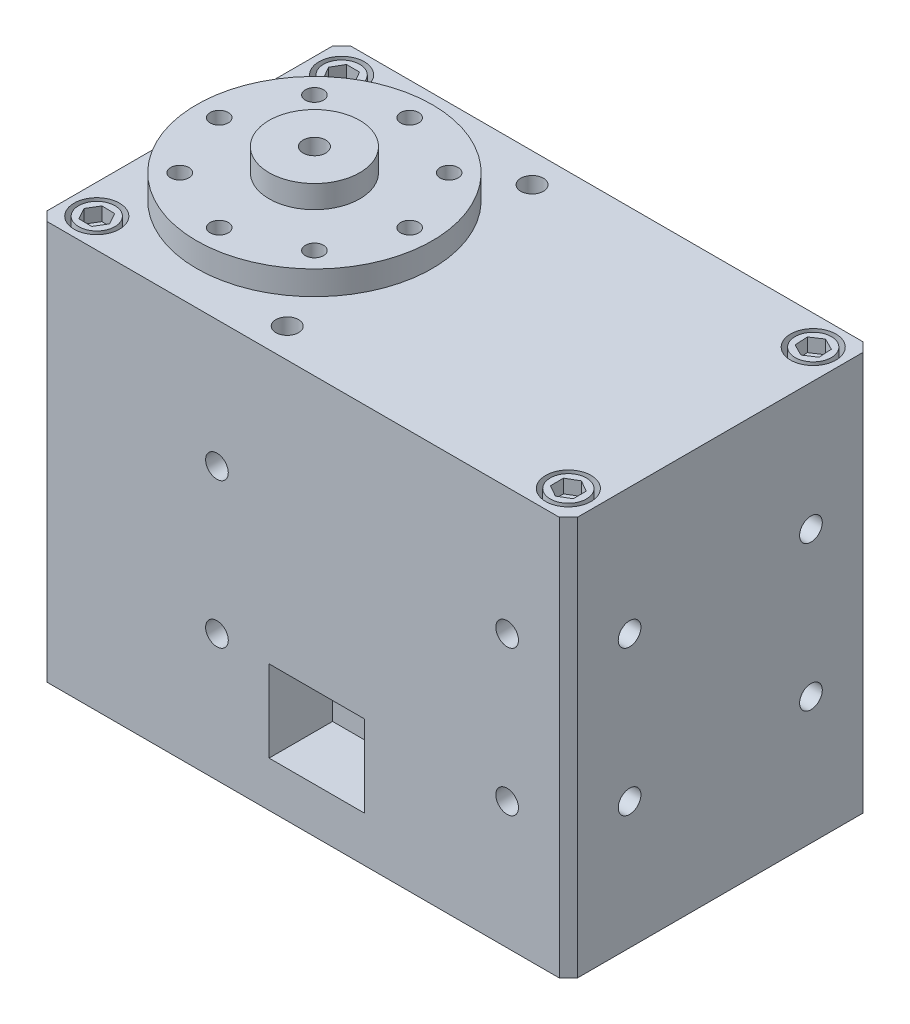
SolidWorks part; units mm, degrees
ref_plane "Front Plane" through (0, 0, 0) normal (0, 0, 1) x (1, 0, 0)
ref_plane "Top Plane" through (0, 0, 0) normal (0, 1, 0) x (1, 0, 0)
ref_plane "Right Plane" through (0, 0, 0) normal (1, 0, 0) x (0, 0, -1)
sketch "Sketch1" plane through (0, 0, 0) normal (0, 1, 0) x (1, 0, 0)
  line L0 (0, 0) -> (0, -23.2365) construction
  line L1 (0, 0) -> (40.4792, 0) construction
  line L2 (-29.25, -15.75) -> (-28.25, -16.75)
  line L3 (-28.25, 16.75) -> (28.25, 16.75)
  line L4 (-29.25, 15.75) -> (-29.25, -15.75)
  line L5 (-28.25, -16.75) -> (28.25, -16.75)
  line L6 (29.25, 15.75) -> (29.25, -15.75)
  line L7 (-29.25, 16.75) -> (29.25, -16.75) construction
  line L8 (-29.25, -16.75) -> (29.25, 16.75) construction
  line L9 (-29.25, 15.75) -> (-28.25, 16.75)
  line L10 (28.25, -16.75) -> (29.25, -15.75)
  line L11 (28.25, 16.75) -> (29.25, 15.75)
  line L12 (26, 0) -> (-26, 0) construction
  line L13 (-26, -13.5) -> (-26, 13.5) construction
  circle A0 centre (-26, -13.5) radius 2.5658 construction
  point P19 (0, 0)
  point P22 (-26, 0)
  dimension "D1" = 33.5
  dimension "D2" = 58.5
  dimension "D3" = 52
  dimension "D4" = 27
extrude "Boss-Extrude1" add sketch "Sketch1" along normal blind 44
sketch "Sketch2" plane through (0, 44, 0) normal (0, 1, 0) x (1, 0, 0)
  line L0 (0, 0) -> (-22.564, 0) construction
  line L1 (26, 0) -> (-26, 0) construction
  line L2 (-26, -13.5) -> (-26, 13.5) construction
  line L3 (-26, 13.5) -> (-15.5, 13.5) construction
  line L4 (-15.5, 13.5) -> (-15.5, -13.5) construction
  circle A0 centre (-15.5, 0) radius 13
  circle A1 centre (-15.5, 0) radius 10.5 construction
  circle A2 centre (-15.5, 10.5) radius 1
  circle A3 centre (-8.0754, 7.4246) radius 1
  circle A4 centre (-5, 0) radius 1
  circle A5 centre (-8.0754, -7.4246) radius 1
  circle A6 centre (-15.5, -10.5) radius 1
  circle A7 centre (-22.9246, -7.4246) radius 1
  circle A8 centre (-26, 0) radius 1
  circle A9 centre (-22.9246, 7.4246) radius 1
  point P6 (0, 0)
  point P9 (-26, 0)
  point P17 (-15.5, 0)
  point P34 (-15.5, 0)
  dimension "D4" = 26
  dimension "D5" = 21
  dimension "D6" = 2
  dimension "D1" = 52
  dimension "D2" = 27
  dimension "D3" = 10.5
  dimension "D7" = 8
extrude "Boss-Extrude2" add sketch "Sketch2" along normal blind 2.65
sketch "Sketch3" plane through (0, 46.65, 0) normal (0, 1, 0) x (1, 0, 0)
  line L0 (-26, 0) -> (-5, 0) construction
  circle A0 centre (-15.5, 0) radius 5
  circle A1 centre (-15.5, 0) radius 1.25
  dimension "D1" = 10
  dimension "D2" = 2.5
extrude "Boss-Extrude3" add sketch "Sketch3" along normal blind 2.5
sketch "Sketch4" plane through (0, 44, 0) normal (0, 1, 0) x (1, 0, 0)
  line L0 (-26, 0) -> (26, 0) construction
  line L1 (-26, -13.5) -> (-26, 13.5) construction
  line L2 (-28.5, 0) -> (-28.5, 19.8485) construction
  line L3 (0, 0) -> (0, 10.5385) construction
  line L4 (28.5, 0) -> (28.5, 19.8485) construction
  line L5 (26, -13.5) -> (26, 13.5) construction
  line L6 (-26, 13.5) -> (-5, 13.5) construction
  circle A0 centre (-15.5, 0) radius 13 construction
  circle A1 centre (-15.5, 0) radius 13 construction
  circle A2 centre (-26, 13.5) radius 2.5
  circle A3 centre (-26, -13.5) radius 2.5
  circle A4 centre (26, -13.5) radius 2.5
  circle A5 centre (26, 13.5) radius 2.5
  circle A6 centre (-5, 13.5) radius 1.25
  circle A7 centre (-5, -13.5) radius 1.25
  point P4 (0, 0)
  point P8 (-26, 0)
  dimension "D4" = 2.5
  dimension "D1" = 52
  dimension "D2" = 27
  dimension "D3" = 21
extrude "Cut-Extrude1" cut sketch "Sketch4" against normal blind 2
sketch "Sketch5" plane through (0, 0, 16.75) normal (0, 0, 1) x (1, 0, 0)
  line L0 (-29.25, 22) -> (29.25, 22) construction
  line L1 (-29.25, 44) -> (-29.25, 0) construction
  line L2 (29.25, 44) -> (29.25, 0) construction
  line L3 (0, 44) -> (0, 0) construction
  line L4 (-28.25, 44) -> (28.25, 44) construction
  line L5 (-15.5, 49.15) -> (-15.5, 0) construction
  line L6 (-14.25, 49.15) -> (-16.75, 49.15) construction
  line L7 (-28.25, 0) -> (28.25, 0) construction
  line L8 (-9.5, 33.3303) -> (-9.5, 11.2546) construction
  line L9 (29.25, 14) -> (29.25, 30)
  line L10 (29.25, 30) -> (-22.2859, 30) construction
  line L11 (29.25, 14) -> (-19.9032, 14) construction
  line L12 (-9.5, 18.7966) -> (22.5, 18.7966) construction
  line L13 (6.5, 18.7966) -> (6.5, 36.282) construction
  line L14 (22.5, 33.3303) -> (22.5, 11.2546) construction
  circle A0 centre (-9.5, 30) radius 1.25
  circle A1 centre (-9.5, 14) radius 1.25
  circle A2 centre (22.5, 14) radius 1.25
  circle A3 centre (22.5, 30) radius 1.25
  point P22 (29.25, 22)
  dimension "D3" = 2.5
  dimension "D1" = 6
  dimension "D2" = 16
  dimension "D4" = 32
extrude "Cut-Extrude2" cut sketch "Sketch5" against normal blind 2 contours A0 | A1 | A3 | A2
sketch "Sketch6" plane through (0, 0, 0) normal (0, -1, 0) x (1, 0, 0)
  line L0 (0, 0) -> (-29.25, 0) construction
  line L1 (-29.25, -15.75) -> (-29.25, 15.75) construction
  line L2 (-29.25, 0) -> (-15.5, 0) construction
  circle A0 centre (-15.5, 0) radius 13
  circle A1 centre (-15.5, 0) radius 10.5 construction
  circle A2 centre (-5, 0) radius 1.25
  circle A3 centre (-8.0754, -7.4246) radius 1.25
  circle A4 centre (-15.5, -10.5) radius 1.25
  circle A5 centre (-22.9246, -7.4246) radius 1.25
  circle A6 centre (-26, 0) radius 1.25
  circle A7 centre (-22.9246, 7.4246) radius 1.25
  circle A8 centre (-15.5, 10.5) radius 1.25
  circle A9 centre (-8.0754, 7.4246) radius 1.25
  point P26 (-15.5, 0)
  dimension "D2" = 26
  dimension "D3" = 21
  dimension "D4" = 2.5
  dimension "D1" = 13.75
  dimension "D5" = 8
extrude "Boss-Extrude4" add sketch "Sketch6" along normal blind 2.5
sketch "Sketch7" plane through (0, 0, 0) normal (0, -1, 0) x (1, 0, 0)
  line L0 (-26, 0) -> (26, 0) construction
  line L1 (-26, -13.5) -> (-26, 13.5) construction
  line L2 (0, 0) -> (0, 13.5) construction
  line L3 (26, -13.5) -> (26, 13.5) construction
  circle A0 centre (-26, 13.5) radius 2.5
  circle A1 centre (-26, -13.5) radius 2.5
  circle A2 centre (26, -13.5) radius 2.5
  circle A3 centre (26, 13.5) radius 2.5
  point P4 (0, 0)
  point P8 (-26, 0)
  dimension "D3" = 5
  dimension "D1" = 52
  dimension "D2" = 27
extrude "Cut-Extrude3" cut sketch "Sketch7" against normal blind 2.5
sketch "Sketch8" plane through (29.25, 0, 0) normal (1, 0, 0) x (0, 0, -1)
  line L0 (-15.75, 22) -> (16.75, 22) construction
  line L1 (-15.75, 44) -> (-15.75, 0) construction
  line L2 (16.75, 44) -> (16.75, 0) construction
  line L3 (0, 44) -> (0, 0) construction
  line L4 (-15.75, 44) -> (15.75, 44) construction
  line L5 (-13, 0) -> (13, 0) construction
  line L6 (0, 22) -> (0, 14) construction
  line L7 (-10, 14) -> (10, 14) construction
  line L8 (-10, 30) -> (10, 30) construction
  circle A0 centre (-10, 14) radius 1.25
  circle A1 centre (10, 14) radius 1.25
  circle A2 centre (10, 30) radius 1.25
  circle A3 centre (-10, 30) radius 1.25
  point P17 (0, 14)
  point P23 (0, 30)
  dimension "D3" = 2.5
  dimension "D1" = 8
  dimension "D2" = 20
extrude "Cut-Extrude4" cut sketch "Sketch8" against normal blind 2.5
sketch "Sketch9" plane through (-29.25, 0, 0) normal (-1, 0, 0) x (0, 0, 1)
  line L0 (0, 44) -> (0, 0) construction
  line L1 (-15.75, 44) -> (15.75, 44) construction
  line L2 (0, 22) -> (-15.75, 22) construction
  line L3 (-15.75, 44) -> (-15.75, 0) construction
  line L4 (0, 22) -> (0, 30) construction
  line L5 (-10, 30) -> (10, 30) construction
  circle A0 centre (-10, 30) radius 1.25
  circle A1 centre (10, 30) radius 1.25
  point P13 (0, 30)
  dimension "D3" = 2.5
  dimension "D1" = 8
  dimension "D2" = 20
extrude "Cut-Extrude5" cut sketch "Sketch9" against normal blind 2.5
sketch "Sketch10" plane through (0, 0, 16.75) normal (0, 0, 1) x (1, 0, 0)
  line L0 (0, 0) -> (0, 44) construction
  line L1 (-28.25, 44) -> (28.25, 44) construction
  line L2 (6.75, 14) -> (6.75, 5)
  line L3 (29.25, 44) -> (29.25, 0) construction
  line L4 (-3.75, 14) -> (-3.75, 5)
  line L5 (-29.25, 44) -> (-29.25, 0) construction
  line L6 (-3.75, 14) -> (6.75, 14)
  line L7 (-3.75, 5) -> (6.75, 5)
  dimension "D1" = 22.5
  dimension "D2" = 25.5
  dimension "D3" = 9
extrude "Cut-Extrude6" cut sketch "Sketch10" against normal blind 7
ref_plane "Plane1" through (0, 0, 0) normal (0, 0, 1) x (1, 0, 0)
mirror "Mirror1" about plane through (0, 0, 0) normal (0, 0, 1) of "Cut-Extrude6"
mirror "Mirror2" about plane through (0, 0, 0) normal (0, 0, 1) of "Cut-Extrude2"
sketch "Sketch11" plane through (0, -2.5, 0) normal (0, -1, 0) x (1, 0, 0)
  circle A0 centre (-15.5, 0) radius 13
extrude "Cut-Extrude7" cut sketch "Sketch11" against normal blind 2.5
sketch "Sketch13" plane through (0, 42, 0) normal (0, 1, 0) x (1, 0, 0)
  circle A0 centre (-26, 13.5) radius 2
  circle A1 centre (-26, -13.5) radius 2
  circle A2 centre (26, 13.5) radius 2
  circle A3 centre (26, -13.5) radius 2
  dimension "D1" = 4
extrude "Boss-Extrude5" add sketch "Sketch13" along normal blind 2
sketch "Sketch14" plane through (0, 44, 0) normal (0, 1, 0) x (1, 0, 0)
  line L1 (-27.4434, 13.5) -> (-26.7217, 12.25)
  line L2 (-26.7217, 12.25) -> (-25.2783, 12.25)
  line L3 (-25.2783, 12.25) -> (-24.5566, 13.5)
  line L4 (-24.5566, 13.5) -> (-25.2783, 14.75)
  line L5 (-25.2783, 14.75) -> (-26.7217, 14.75)
  line L6 (-26.7217, 14.75) -> (-27.4434, 13.5)
  line L7 (24.7095, 14.1466) -> (24.7948, 12.7057)
  line L8 (24.7948, 12.7057) -> (26.0853, 12.0591)
  line L9 (26.0853, 12.0591) -> (27.2905, 12.8534)
  line L10 (27.2905, 12.8534) -> (27.2052, 14.2943)
  line L11 (27.2052, 14.2943) -> (25.9147, 14.9409)
  line L12 (25.9147, 14.9409) -> (24.7095, 14.1466)
  line L13 (-26.6949, -12.2349) -> (-27.443, -13.4693)
  line L14 (-27.443, -13.4693) -> (-26.7481, -14.7344)
  line L15 (-26.7481, -14.7344) -> (-25.3051, -14.7651)
  line L16 (-25.3051, -14.7651) -> (-24.557, -13.5307)
  line L17 (-24.557, -13.5307) -> (-25.2519, -12.2656)
  line L18 (-25.2519, -12.2656) -> (-26.6949, -12.2349)
  line L19 (24.7542, -14.2289) -> (26.0084, -14.9434)
  line L20 (26.0084, -14.9434) -> (27.2542, -14.2144)
  line L21 (27.2542, -14.2144) -> (27.2458, -12.7711)
  line L22 (27.2458, -12.7711) -> (25.9916, -12.0566)
  line L23 (25.9916, -12.0566) -> (24.7458, -12.7856)
  line L24 (24.7458, -12.7856) -> (24.7542, -14.2289)
  circle A0 centre (-26, 13.5) radius 1.25 construction
  circle A1 centre (26, 13.5) radius 1.25 construction
  circle A2 centre (-26, -13.5) radius 1.25 construction
  circle A3 centre (26, -13.5) radius 1.25 construction
  dimension "D1" = 2.5
extrude "Cut-Extrude8" cut sketch "Sketch14" against normal blind 1.5
ref_plane "Plane2" through (0, 22, 0) normal (0, -1, 0) x (-1, 0, 0)
sketch "Sketch15" plane through (0, 2.5, 0) normal (0, -1, 0) x (1, 0, 0)
  circle A0 centre (-26, 13.5) radius 2
  circle A1 centre (26, 13.5) radius 2
  circle A2 centre (-26, -13.5) radius 2
  circle A3 centre (26, -13.5) radius 2
  dimension "D1" = 4
extrude "Boss-Extrude6" add sketch "Sketch15" along normal blind 2.5
sketch "Sketch16" plane through (0, 0, 0) normal (0, -1, 0) x (1, 0, 0)
  line L1 (-26, 12.0566) -> (-24.75, 12.7783)
  line L2 (-24.75, 12.7783) -> (-24.75, 14.2217)
  line L3 (-24.75, 14.2217) -> (-26, 14.9434)
  line L4 (-26, 14.9434) -> (-27.25, 14.2217)
  line L5 (-27.25, 14.2217) -> (-27.25, 12.7783)
  line L6 (-27.25, 12.7783) -> (-26, 12.0566)
  line L7 (26, 12.0566) -> (27.25, 12.7783)
  line L8 (27.25, 12.7783) -> (27.25, 14.2217)
  line L9 (27.25, 14.2217) -> (26, 14.9434)
  line L10 (26, 14.9434) -> (24.75, 14.2217)
  line L11 (24.75, 14.2217) -> (24.75, 12.7783)
  line L12 (24.75, 12.7783) -> (26, 12.0566)
  line L13 (26, -14.9434) -> (27.25, -14.2217)
  line L14 (27.25, -14.2217) -> (27.25, -12.7783)
  line L15 (27.25, -12.7783) -> (26, -12.0566)
  line L16 (26, -12.0566) -> (24.75, -12.7783)
  line L17 (24.75, -12.7783) -> (24.75, -14.2217)
  line L18 (24.75, -14.2217) -> (26, -14.9434)
  line L19 (-26, -14.9434) -> (-24.75, -14.2217)
  line L20 (-24.75, -14.2217) -> (-24.75, -12.7783)
  line L21 (-24.75, -12.7783) -> (-26, -12.0566)
  line L22 (-26, -12.0566) -> (-27.25, -12.7783)
  line L23 (-27.25, -12.7783) -> (-27.25, -14.2217)
  line L24 (-27.25, -14.2217) -> (-26, -14.9434)
  circle A0 centre (-26, 13.5) radius 1.25 construction
  circle A1 centre (26, 13.5) radius 1.25 construction
  circle A2 centre (26, -13.5) radius 1.25 construction
  circle A3 centre (-26, -13.5) radius 1.25 construction
  dimension "D1" = 2.5
extrude "Cut-Extrude9" cut sketch "Sketch16" against normal blind 1.5
sketch "Sketch17" plane through (0, 44, 0) normal (0, 1, 0) x (1, 0, 0)
  line L0 (25.25, 9.601) -> (25.25, -9.3165) construction
  line L1 (29.25, -15.75) -> (29.25, 15.75) construction
  line L2 (25.25, 6.0422) -> (25.25, -5.7578)
  line L3 (17.75, -5.7578) -> (17.75, 6.0422)
  line L5 (24.25, 7.0422) -> (18.75, 7.0422)
  line L6 (24.25, -6.7578) -> (18.75, -6.7578)
  line L7 (21.5, -6.7578) -> (21.5, 7.0422) construction
  line L8 (23.9695, -6.7578) -> (23.9695, 7.0422) construction
  arc A0 (25.25, -5.7578) -> (24.25, -6.7578) centre (24.25, -5.7578) cw
  arc A1 (18.75, -6.7578) -> (17.75, -5.7578) centre (18.75, -5.7578) cw
  arc A2 (25.25, 6.0422) -> (24.25, 7.0422) centre (24.25, 6.0422) ccw
  arc A3 (18.75, 7.0422) -> (17.75, 6.0422) centre (18.75, 6.0422) ccw
  text T0 "DYNAMIXEL" font "Century Gothic" height 1.7
  text T1 "XM54-W150-R" font "Century Gothic" height 1
  point P7 (25.25, 0.1422)
  point P10 (17.75, -0.0518)
  point P11 (25.25, -6.7578)
  point P17 (25.25, 7.0422)
  dimension "D4" = 1
  dimension "D1" = 4
  dimension "D2" = 13.8
  dimension "D3" = 7.5
